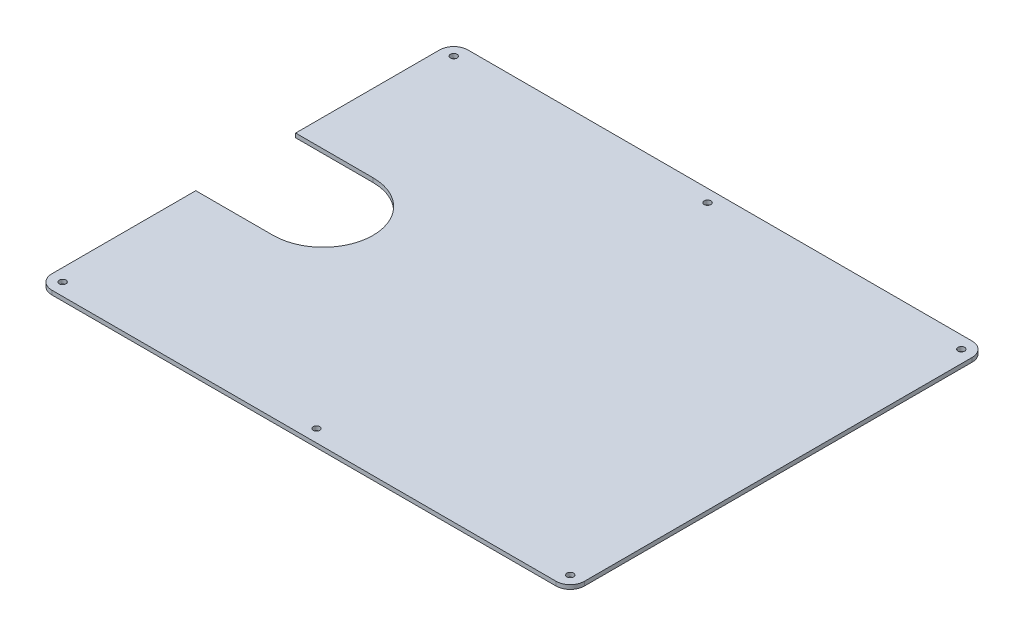
SolidWorks part; units mm, degrees
ref_plane "Front" through (0, 0, 0) normal (0, 0, 1) x (1, 0, 0)
ref_plane "Top" through (0, 0, 0) normal (0, 1, 0) x (1, 0, 0)
ref_plane "Right" through (0, 0, 0) normal (1, 0, 0) x (0, 0, -1)
sketch "Croquis1" plane through (0, 0, 0) normal (0, 1, 0) x (1, 0, 0)
  line L0 (0, 0) -> (50000, 0) construction
  line L1 (-303, 250) -> (303, 250)
  line L2 (-320, 233) -> (-320, -233)
  line L3 (-303, -250) -> (303, -250)
  line L4 (320, 233) -> (320, -233)
  line L5 (-320, 250) -> (320, -250) construction
  line L6 (-320, -250) -> (320, 250) construction
  line L7 (-305, -235) -> (305, -235) construction
  line L8 (-305, -235) -> (-305, 235) construction
  line L9 (-305, 235) -> (305, 235) construction
  line L10 (305, -235) -> (305, 235) construction
  line L11 (-305, -235) -> (305, 235) construction
  line L12 (-305, 235) -> (305, -235) construction
  line L13 (0, 0) -> (0, 50000) construction
  arc A0 (-320, -233) -> (-303, -250) centre (-303, -233) ccw
  arc A1 (320, -233) -> (303, -250) centre (303, -233) cw
  arc A2 (303, 250) -> (320, 233) centre (303, 233) cw
  arc A3 (-303, 250) -> (-320, 233) centre (-303, 233) ccw
  circle A4 centre (0, 235) radius 4
  circle A5 centre (305, 235) radius 4
  circle A6 centre (-305, 235) radius 4
  circle A7 centre (0, -235) radius 4
  circle A8 centre (305, -235) radius 4
  circle A9 centre (-305, -235) radius 4
  point P0 (0, 0)
  point P18 (0, 0)
  dimension "D3" = 17
  dimension "D6" = 8
  dimension "D1" = 640
  dimension "D2" = 500
  dimension "D4" = 15
  dimension "D5" = 15
extrude "Saliente-Extruir1" add sketch "Croquis1" along normal blind 5
sketch "Croquis3" plane through (0, 0, 0) normal (0, -1, 0) x (1, 0, 0)
  line L0 (-227, 60) -> (-320, 60)
  line L1 (-320, -233) -> (-320, 233) construction
  line L2 (-320, 60) -> (-320, -60)
  line L3 (-320, -60) -> (-227, -60)
  arc A0 (-227, 60) -> (-227, -60) centre (-227, 0) cw
  dimension "D1" = 60
  dimension "D2" = 93
extrude "Cortar-Extruir2" cut sketch "Croquis3" against normal through all
